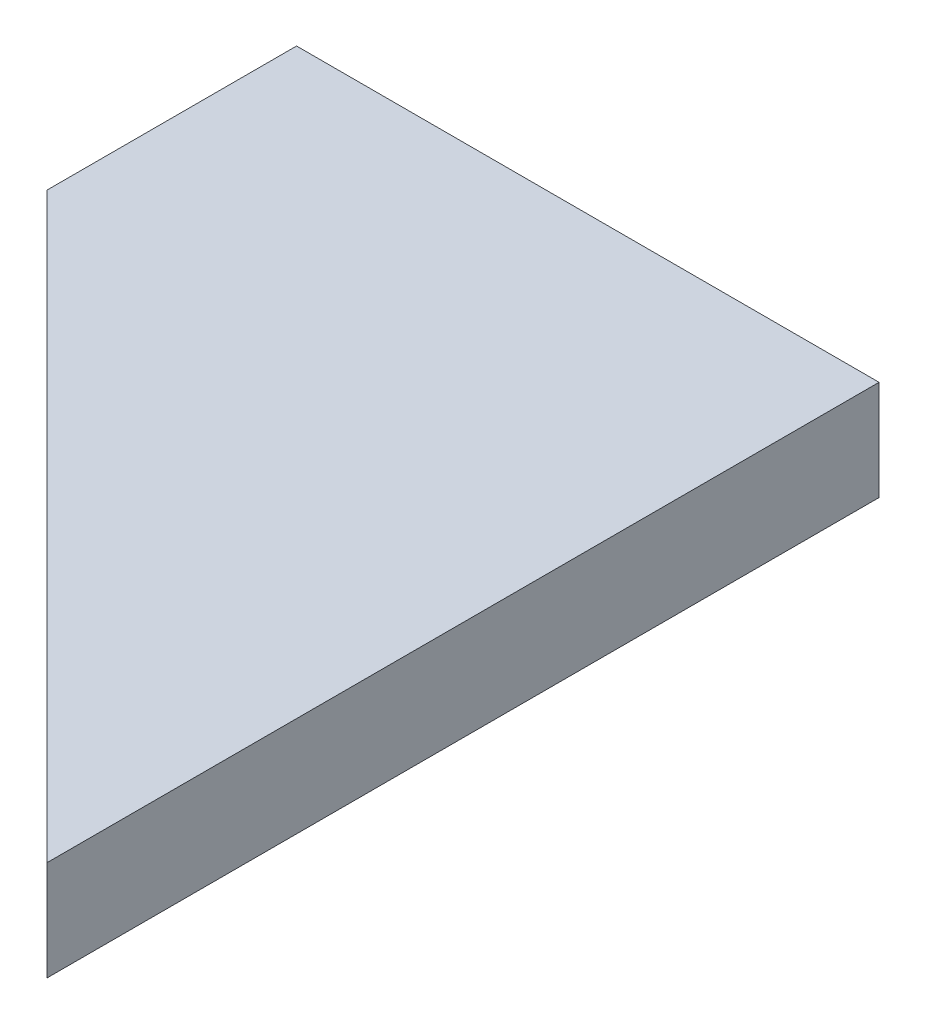
SolidWorks part; units mm, degrees
ref_plane "Alzado" through (0, 0, 0) normal (0, 0, 1) x (1, 0, 0)
ref_plane "Planta" through (0, 0, 0) normal (0, 1, 0) x (1, 0, 0)
ref_plane "Vista lateral" through (0, 0, 0) normal (1, 0, 0) x (0, 0, -1)
sketch "Croquis1" plane through (0, 0, 0) normal (0, 1, 0) x (1, 0, 0)
  line L0 (-11.6673, 6.6673) -> (11.6673, -16.6673)
  line L1 (-11.6673, 16.6673) -> (11.6673, 16.6673)
  line L2 (-11.6673, 16.6673) -> (-11.6673, -16.6673) construction
  line L3 (-11.6673, -16.6673) -> (11.6673, -16.6673) construction
  line L4 (11.6673, 16.6673) -> (11.6673, -16.6673)
  line L5 (-11.6673, 16.6673) -> (11.6673, -16.6673) construction
  line L6 (-11.6673, -16.6673) -> (11.6673, 16.6673) construction
  line L7 (-11.6673, 6.6673) -> (-11.6673, 16.6673)
  point P0 (0, 0)
  dimension "D1" = 10
  dimension "D2" = 45
  dimension "D3" = 33
extrude "Saliente-Extruir1" add sketch "Croquis1" along normal blind 4
